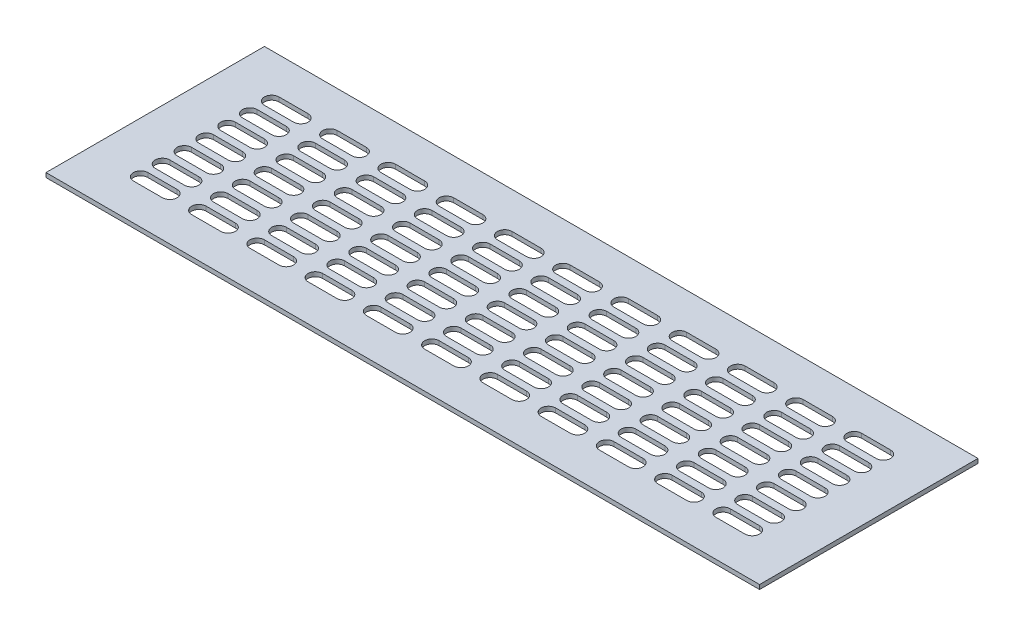
SolidWorks part; units mm, degrees
material "AISI 316 Stainless Steel Sheet (SS)"
ref_plane "Front Plane" through (0, 0, 0) normal (0, 0, 1) x (1, 0, 0)
ref_plane "Top Plane" through (0, 0, 0) normal (0, 1, 0) x (1, 0, 0)
ref_plane "Right Plane" through (0, 0, 0) normal (1, 0, 0) x (0, 0, -1)
sketch "Sketch1" plane through (0, 0, 0) normal (0, 1, 0) x (1, 0, 0)
  line L1 (-245, -75) -> (245, -75)
  line L2 (-245, -75) -> (-245, 75)
  line L3 (-245, 75) -> (245, 75)
  line L4 (245, -75) -> (245, 75)
  line L5 (-245, -75) -> (245, 75) construction
  line L6 (-245, 75) -> (245, -75) construction
  point P0 (0, 0)
  dimension "D1" = 490
  dimension "D2" = 150
extrude "Boss-Extrude1" add sketch "Sketch1" along normal mid plane 3
sketch "Sketch2" plane through (0, 1.5, 0) normal (0, 1, 0) x (1, 0, 0)
  line L0 (-210, 45) -> (-190, 45) construction
  line L1 (-210, 50) -> (-190, 50)
  line L2 (-210, 40) -> (-190, 40)
  line L3 (-245, 75) -> (-245, -75) construction
  line L4 (245, 75) -> (-245, 75) construction
  line L5 (-200, 55.9106) -> (-200, 34.5617) construction
  line L6 (-181.2775, 45) -> (-218.1008, 45) construction
  line L7 (-170, 45) -> (-150, 45) construction
  line L8 (-170, 50) -> (-150, 50)
  line L9 (-170, 40) -> (-150, 40)
  line L10 (-130, 45) -> (-110, 45) construction
  line L11 (-130, 50) -> (-110, 50)
  line L12 (-130, 40) -> (-110, 40)
  line L13 (-90, 45) -> (-70, 45) construction
  line L14 (-90, 50) -> (-70, 50)
  line L15 (-90, 40) -> (-70, 40)
  line L16 (-50, 45) -> (-30, 45) construction
  line L17 (-50, 50) -> (-30, 50)
  line L18 (-50, 40) -> (-30, 40)
  line L19 (-10, 45) -> (10, 45) construction
  line L20 (-10, 50) -> (10, 50)
  line L21 (-10, 40) -> (10, 40)
  line L22 (30, 45) -> (50, 45) construction
  line L23 (30, 50) -> (50, 50)
  line L24 (30, 40) -> (50, 40)
  line L25 (70, 45) -> (90, 45) construction
  line L26 (70, 50) -> (90, 50)
  line L27 (70, 40) -> (90, 40)
  line L28 (110, 45) -> (130, 45) construction
  line L29 (110, 50) -> (130, 50)
  line L30 (110, 40) -> (130, 40)
  line L31 (150, 45) -> (170, 45) construction
  line L32 (150, 50) -> (170, 50)
  line L33 (150, 40) -> (170, 40)
  line L34 (190, 45) -> (210, 45) construction
  line L35 (190, 50) -> (210, 50)
  line L36 (190, 40) -> (210, 40)
  line L37 (-170, 30) -> (-150, 30) construction
  line L38 (-170, 35) -> (-150, 35)
  line L39 (-170, 25) -> (-150, 25)
  line L40 (-130, 30) -> (-110, 30) construction
  line L41 (-130, 35) -> (-110, 35)
  line L42 (-130, 25) -> (-110, 25)
  line L43 (-90, 30) -> (-70, 30) construction
  line L44 (-90, 35) -> (-70, 35)
  line L45 (-90, 25) -> (-70, 25)
  line L46 (-50, 30) -> (-30, 30) construction
  line L47 (-50, 35) -> (-30, 35)
  line L48 (-50, 25) -> (-30, 25)
  line L49 (-10, 30) -> (10, 30) construction
  line L50 (-10, 35) -> (10, 35)
  line L51 (-10, 25) -> (10, 25)
  line L52 (30, 30) -> (50, 30) construction
  line L53 (30, 35) -> (50, 35)
  line L54 (30, 25) -> (50, 25)
  line L55 (70, 30) -> (90, 30) construction
  line L56 (70, 35) -> (90, 35)
  line L57 (70, 25) -> (90, 25)
  line L58 (110, 30) -> (130, 30) construction
  line L59 (110, 35) -> (130, 35)
  line L60 (110, 25) -> (130, 25)
  line L61 (150, 30) -> (170, 30) construction
  line L62 (150, 35) -> (170, 35)
  line L63 (150, 25) -> (170, 25)
  line L64 (190, 30) -> (210, 30) construction
  line L65 (190, 35) -> (210, 35)
  line L66 (190, 25) -> (210, 25)
  line L67 (-170, 15) -> (-150, 15) construction
  line L68 (-170, 20) -> (-150, 20)
  line L69 (-170, 10) -> (-150, 10)
  line L70 (-130, 15) -> (-110, 15) construction
  line L71 (-130, 20) -> (-110, 20)
  line L72 (-130, 10) -> (-110, 10)
  line L73 (-90, 15) -> (-70, 15) construction
  line L74 (-90, 20) -> (-70, 20)
  line L75 (-90, 10) -> (-70, 10)
  line L76 (-50, 15) -> (-30, 15) construction
  line L77 (-50, 20) -> (-30, 20)
  line L78 (-50, 10) -> (-30, 10)
  line L79 (-10, 15) -> (10, 15) construction
  line L80 (-10, 20) -> (10, 20)
  line L81 (-10, 10) -> (10, 10)
  line L82 (30, 15) -> (50, 15) construction
  line L83 (30, 20) -> (50, 20)
  line L84 (30, 10) -> (50, 10)
  line L85 (70, 15) -> (90, 15) construction
  line L86 (70, 20) -> (90, 20)
  line L87 (70, 10) -> (90, 10)
  line L88 (110, 15) -> (130, 15) construction
  line L89 (110, 20) -> (130, 20)
  line L90 (110, 10) -> (130, 10)
  line L91 (150, 15) -> (170, 15) construction
  line L92 (150, 20) -> (170, 20)
  line L93 (150, 10) -> (170, 10)
  line L94 (190, 15) -> (210, 15) construction
  line L95 (190, 20) -> (210, 20)
  line L96 (190, 10) -> (210, 10)
  line L97 (-170, 0) -> (-150, 0) construction
  line L98 (-170, 5) -> (-150, 5)
  line L99 (-170, -5) -> (-150, -5)
  line L100 (-130, 0) -> (-110, 0) construction
  line L101 (-130, 5) -> (-110, 5)
  line L102 (-130, -5) -> (-110, -5)
  line L103 (-90, 0) -> (-70, 0) construction
  line L104 (-90, 5) -> (-70, 5)
  line L105 (-90, -5) -> (-70, -5)
  line L106 (-50, 0) -> (-30, 0) construction
  line L107 (-50, 5) -> (-30, 5)
  line L108 (-50, -5) -> (-30, -5)
  line L109 (-10, 0) -> (10, 0) construction
  line L110 (-10, 5) -> (10, 5)
  line L111 (-10, -5) -> (10, -5)
  line L112 (30, 0) -> (50, 0) construction
  line L113 (30, 5) -> (50, 5)
  line L114 (30, -5) -> (50, -5)
  line L115 (70, 0) -> (90, 0) construction
  line L116 (70, 5) -> (90, 5)
  line L117 (70, -5) -> (90, -5)
  line L118 (110, 0) -> (130, 0) construction
  line L119 (110, 5) -> (130, 5)
  line L120 (110, -5) -> (130, -5)
  line L121 (150, 0) -> (170, 0) construction
  line L122 (150, 5) -> (170, 5)
  line L123 (150, -5) -> (170, -5)
  line L124 (190, 0) -> (210, 0) construction
  line L125 (190, 5) -> (210, 5)
  line L126 (190, -5) -> (210, -5)
  line L127 (-170, -15) -> (-150, -15) construction
  line L128 (-170, -10) -> (-150, -10)
  line L129 (-170, -20) -> (-150, -20)
  line L130 (-130, -15) -> (-110, -15) construction
  line L131 (-130, -10) -> (-110, -10)
  line L132 (-130, -20) -> (-110, -20)
  line L133 (-90, -15) -> (-70, -15) construction
  line L134 (-90, -10) -> (-70, -10)
  line L135 (-90, -20) -> (-70, -20)
  line L136 (-50, -15) -> (-30, -15) construction
  line L137 (-50, -10) -> (-30, -10)
  line L138 (-50, -20) -> (-30, -20)
  line L139 (-10, -15) -> (10, -15) construction
  line L140 (-10, -10) -> (10, -10)
  line L141 (-10, -20) -> (10, -20)
  line L142 (30, -15) -> (50, -15) construction
  line L143 (30, -10) -> (50, -10)
  line L144 (30, -20) -> (50, -20)
  line L145 (70, -15) -> (90, -15) construction
  line L146 (70, -10) -> (90, -10)
  line L147 (70, -20) -> (90, -20)
  line L148 (110, -15) -> (130, -15) construction
  line L149 (110, -10) -> (130, -10)
  line L150 (110, -20) -> (130, -20)
  line L151 (150, -15) -> (170, -15) construction
  line L152 (150, -10) -> (170, -10)
  line L153 (150, -20) -> (170, -20)
  line L154 (190, -15) -> (210, -15) construction
  line L155 (190, -10) -> (210, -10)
  line L156 (190, -20) -> (210, -20)
  line L157 (-170, -30) -> (-150, -30) construction
  line L158 (-170, -25) -> (-150, -25)
  line L159 (-170, -35) -> (-150, -35)
  line L160 (-130, -30) -> (-110, -30) construction
  line L161 (-130, -25) -> (-110, -25)
  line L162 (-130, -35) -> (-110, -35)
  line L163 (-90, -30) -> (-70, -30) construction
  line L164 (-90, -25) -> (-70, -25)
  line L165 (-90, -35) -> (-70, -35)
  line L166 (-50, -30) -> (-30, -30) construction
  line L167 (-50, -25) -> (-30, -25)
  line L168 (-50, -35) -> (-30, -35)
  line L169 (-10, -30) -> (10, -30) construction
  line L170 (-10, -25) -> (10, -25)
  line L171 (-10, -35) -> (10, -35)
  line L172 (30, -30) -> (50, -30) construction
  line L173 (30, -25) -> (50, -25)
  line L174 (30, -35) -> (50, -35)
  line L175 (70, -30) -> (90, -30) construction
  line L176 (70, -25) -> (90, -25)
  line L177 (70, -35) -> (90, -35)
  line L178 (110, -30) -> (130, -30) construction
  line L179 (110, -25) -> (130, -25)
  line L180 (110, -35) -> (130, -35)
  line L181 (150, -30) -> (170, -30) construction
  line L182 (150, -25) -> (170, -25)
  line L183 (150, -35) -> (170, -35)
  line L184 (190, -30) -> (210, -30) construction
  line L185 (190, -25) -> (210, -25)
  line L186 (190, -35) -> (210, -35)
  line L187 (-170, -45) -> (-150, -45) construction
  line L188 (-170, -40) -> (-150, -40)
  line L189 (-170, -50) -> (-150, -50)
  line L190 (-130, -45) -> (-110, -45) construction
  line L191 (-130, -40) -> (-110, -40)
  line L192 (-130, -50) -> (-110, -50)
  line L193 (-90, -45) -> (-70, -45) construction
  line L194 (-90, -40) -> (-70, -40)
  line L195 (-90, -50) -> (-70, -50)
  line L196 (-50, -45) -> (-30, -45) construction
  line L197 (-50, -40) -> (-30, -40)
  line L198 (-50, -50) -> (-30, -50)
  line L199 (-10, -45) -> (10, -45) construction
  line L200 (-10, -40) -> (10, -40)
  line L201 (-10, -50) -> (10, -50)
  line L202 (30, -45) -> (50, -45) construction
  line L203 (30, -40) -> (50, -40)
  line L204 (30, -50) -> (50, -50)
  line L205 (70, -45) -> (90, -45) construction
  line L206 (70, -40) -> (90, -40)
  line L207 (70, -50) -> (90, -50)
  line L208 (110, -45) -> (130, -45) construction
  line L209 (110, -40) -> (130, -40)
  line L210 (110, -50) -> (130, -50)
  line L211 (150, -45) -> (170, -45) construction
  line L212 (150, -40) -> (170, -40)
  line L213 (150, -50) -> (170, -50)
  line L214 (190, -45) -> (210, -45) construction
  line L215 (190, -40) -> (210, -40)
  line L216 (190, -50) -> (210, -50)
  line L217 (-210, 30) -> (-190, 30) construction
  line L218 (-210, 35) -> (-190, 35)
  line L219 (-210, 25) -> (-190, 25)
  line L220 (-210, 15) -> (-190, 15) construction
  line L221 (-210, 20) -> (-190, 20)
  line L222 (-210, 10) -> (-190, 10)
  line L223 (-210, 0) -> (-190, 0) construction
  line L224 (-210, 5) -> (-190, 5)
  line L225 (-210, -5) -> (-190, -5)
  line L226 (-210, -15) -> (-190, -15) construction
  line L227 (-210, -10) -> (-190, -10)
  line L228 (-210, -20) -> (-190, -20)
  line L229 (-210, -30) -> (-190, -30) construction
  line L230 (-210, -25) -> (-190, -25)
  line L231 (-210, -35) -> (-190, -35)
  line L232 (-210, -45) -> (-190, -45) construction
  line L233 (-210, -40) -> (-190, -40)
  line L234 (-210, -50) -> (-190, -50)
  arc A0 (-210, 50) -> (-210, 40) centre (-210, 45) ccw
  arc A1 (-190, 40) -> (-190, 50) centre (-190, 45) ccw
  arc A2 (-170, 50) -> (-170, 40) centre (-170, 45) ccw
  arc A3 (-150, 40) -> (-150, 50) centre (-150, 45) ccw
  arc A4 (-130, 50) -> (-130, 40) centre (-130, 45) ccw
  arc A5 (-110, 40) -> (-110, 50) centre (-110, 45) ccw
  arc A6 (-90, 50) -> (-90, 40) centre (-90, 45) ccw
  arc A7 (-70, 40) -> (-70, 50) centre (-70, 45) ccw
  arc A8 (-50, 50) -> (-50, 40) centre (-50, 45) ccw
  arc A9 (-30, 40) -> (-30, 50) centre (-30, 45) ccw
  arc A10 (-10, 50) -> (-10, 40) centre (-10, 45) ccw
  arc A11 (10, 40) -> (10, 50) centre (10, 45) ccw
  arc A12 (30, 50) -> (30, 40) centre (30, 45) ccw
  arc A13 (50, 40) -> (50, 50) centre (50, 45) ccw
  arc A14 (70, 50) -> (70, 40) centre (70, 45) ccw
  arc A15 (90, 40) -> (90, 50) centre (90, 45) ccw
  arc A16 (110, 50) -> (110, 40) centre (110, 45) ccw
  arc A17 (130, 40) -> (130, 50) centre (130, 45) ccw
  arc A18 (150, 50) -> (150, 40) centre (150, 45) ccw
  arc A19 (170, 40) -> (170, 50) centre (170, 45) ccw
  arc A20 (190, 50) -> (190, 40) centre (190, 45) ccw
  arc A21 (210, 40) -> (210, 50) centre (210, 45) ccw
  arc A22 (-170, 35) -> (-170, 25) centre (-170, 30) ccw
  arc A23 (-150, 25) -> (-150, 35) centre (-150, 30) ccw
  arc A24 (-130, 35) -> (-130, 25) centre (-130, 30) ccw
  arc A25 (-110, 25) -> (-110, 35) centre (-110, 30) ccw
  arc A26 (-90, 35) -> (-90, 25) centre (-90, 30) ccw
  arc A27 (-70, 25) -> (-70, 35) centre (-70, 30) ccw
  arc A28 (-50, 35) -> (-50, 25) centre (-50, 30) ccw
  arc A29 (-30, 25) -> (-30, 35) centre (-30, 30) ccw
  arc A30 (-10, 35) -> (-10, 25) centre (-10, 30) ccw
  arc A31 (10, 25) -> (10, 35) centre (10, 30) ccw
  arc A32 (30, 35) -> (30, 25) centre (30, 30) ccw
  arc A33 (50, 25) -> (50, 35) centre (50, 30) ccw
  arc A34 (70, 35) -> (70, 25) centre (70, 30) ccw
  arc A35 (90, 25) -> (90, 35) centre (90, 30) ccw
  arc A36 (110, 35) -> (110, 25) centre (110, 30) ccw
  arc A37 (130, 25) -> (130, 35) centre (130, 30) ccw
  arc A38 (150, 35) -> (150, 25) centre (150, 30) ccw
  arc A39 (170, 25) -> (170, 35) centre (170, 30) ccw
  arc A40 (190, 35) -> (190, 25) centre (190, 30) ccw
  arc A41 (210, 25) -> (210, 35) centre (210, 30) ccw
  arc A42 (-170, 20) -> (-170, 10) centre (-170, 15) ccw
  arc A43 (-150, 10) -> (-150, 20) centre (-150, 15) ccw
  arc A44 (-130, 20) -> (-130, 10) centre (-130, 15) ccw
  arc A45 (-110, 10) -> (-110, 20) centre (-110, 15) ccw
  arc A46 (-90, 20) -> (-90, 10) centre (-90, 15) ccw
  arc A47 (-70, 10) -> (-70, 20) centre (-70, 15) ccw
  arc A48 (-50, 20) -> (-50, 10) centre (-50, 15) ccw
  arc A49 (-30, 10) -> (-30, 20) centre (-30, 15) ccw
  arc A50 (-10, 20) -> (-10, 10) centre (-10, 15) ccw
  arc A51 (10, 10) -> (10, 20) centre (10, 15) ccw
  arc A52 (30, 20) -> (30, 10) centre (30, 15) ccw
  arc A53 (50, 10) -> (50, 20) centre (50, 15) ccw
  arc A54 (70, 20) -> (70, 10) centre (70, 15) ccw
  arc A55 (90, 10) -> (90, 20) centre (90, 15) ccw
  arc A56 (110, 20) -> (110, 10) centre (110, 15) ccw
  arc A57 (130, 10) -> (130, 20) centre (130, 15) ccw
  arc A58 (150, 20) -> (150, 10) centre (150, 15) ccw
  arc A59 (170, 10) -> (170, 20) centre (170, 15) ccw
  arc A60 (190, 20) -> (190, 10) centre (190, 15) ccw
  arc A61 (210, 10) -> (210, 20) centre (210, 15) ccw
  arc A62 (-170, 5) -> (-170, -5) centre (-170, 0) ccw
  arc A63 (-150, -5) -> (-150, 5) centre (-150, 0) ccw
  arc A64 (-130, 5) -> (-130, -5) centre (-130, 0) ccw
  arc A65 (-110, -5) -> (-110, 5) centre (-110, 0) ccw
  arc A66 (-90, 5) -> (-90, -5) centre (-90, 0) ccw
  arc A67 (-70, -5) -> (-70, 5) centre (-70, 0) ccw
  arc A68 (-50, 5) -> (-50, -5) centre (-50, 0) ccw
  arc A69 (-30, -5) -> (-30, 5) centre (-30, 0) ccw
  arc A70 (-10, 5) -> (-10, -5) centre (-10, 0) ccw
  arc A71 (10, -5) -> (10, 5) centre (10, 0) ccw
  arc A72 (30, 5) -> (30, -5) centre (30, 0) ccw
  arc A73 (50, -5) -> (50, 5) centre (50, 0) ccw
  arc A74 (70, 5) -> (70, -5) centre (70, 0) ccw
  arc A75 (90, -5) -> (90, 5) centre (90, 0) ccw
  arc A76 (110, 5) -> (110, -5) centre (110, 0) ccw
  arc A77 (130, -5) -> (130, 5) centre (130, 0) ccw
  arc A78 (150, 5) -> (150, -5) centre (150, 0) ccw
  arc A79 (170, -5) -> (170, 5) centre (170, 0) ccw
  arc A80 (190, 5) -> (190, -5) centre (190, 0) ccw
  arc A81 (210, -5) -> (210, 5) centre (210, 0) ccw
  arc A82 (-170, -10) -> (-170, -20) centre (-170, -15) ccw
  arc A83 (-150, -20) -> (-150, -10) centre (-150, -15) ccw
  arc A84 (-130, -10) -> (-130, -20) centre (-130, -15) ccw
  arc A85 (-110, -20) -> (-110, -10) centre (-110, -15) ccw
  arc A86 (-90, -10) -> (-90, -20) centre (-90, -15) ccw
  arc A87 (-70, -20) -> (-70, -10) centre (-70, -15) ccw
  arc A88 (-50, -10) -> (-50, -20) centre (-50, -15) ccw
  arc A89 (-30, -20) -> (-30, -10) centre (-30, -15) ccw
  arc A90 (-10, -10) -> (-10, -20) centre (-10, -15) ccw
  arc A91 (10, -20) -> (10, -10) centre (10, -15) ccw
  arc A92 (30, -10) -> (30, -20) centre (30, -15) ccw
  arc A93 (50, -20) -> (50, -10) centre (50, -15) ccw
  arc A94 (70, -10) -> (70, -20) centre (70, -15) ccw
  arc A95 (90, -20) -> (90, -10) centre (90, -15) ccw
  arc A96 (110, -10) -> (110, -20) centre (110, -15) ccw
  arc A97 (130, -20) -> (130, -10) centre (130, -15) ccw
  arc A98 (150, -10) -> (150, -20) centre (150, -15) ccw
  arc A99 (170, -20) -> (170, -10) centre (170, -15) ccw
  arc A100 (190, -10) -> (190, -20) centre (190, -15) ccw
  arc A101 (210, -20) -> (210, -10) centre (210, -15) ccw
  arc A102 (-170, -25) -> (-170, -35) centre (-170, -30) ccw
  arc A103 (-150, -35) -> (-150, -25) centre (-150, -30) ccw
  arc A104 (-130, -25) -> (-130, -35) centre (-130, -30) ccw
  arc A105 (-110, -35) -> (-110, -25) centre (-110, -30) ccw
  arc A106 (-90, -25) -> (-90, -35) centre (-90, -30) ccw
  arc A107 (-70, -35) -> (-70, -25) centre (-70, -30) ccw
  arc A108 (-50, -25) -> (-50, -35) centre (-50, -30) ccw
  arc A109 (-30, -35) -> (-30, -25) centre (-30, -30) ccw
  arc A110 (-10, -25) -> (-10, -35) centre (-10, -30) ccw
  arc A111 (10, -35) -> (10, -25) centre (10, -30) ccw
  arc A112 (30, -25) -> (30, -35) centre (30, -30) ccw
  arc A113 (50, -35) -> (50, -25) centre (50, -30) ccw
  arc A114 (70, -25) -> (70, -35) centre (70, -30) ccw
  arc A115 (90, -35) -> (90, -25) centre (90, -30) ccw
  arc A116 (110, -25) -> (110, -35) centre (110, -30) ccw
  arc A117 (130, -35) -> (130, -25) centre (130, -30) ccw
  arc A118 (150, -25) -> (150, -35) centre (150, -30) ccw
  arc A119 (170, -35) -> (170, -25) centre (170, -30) ccw
  arc A120 (190, -25) -> (190, -35) centre (190, -30) ccw
  arc A121 (210, -35) -> (210, -25) centre (210, -30) ccw
  arc A122 (-170, -40) -> (-170, -50) centre (-170, -45) ccw
  arc A123 (-150, -50) -> (-150, -40) centre (-150, -45) ccw
  arc A124 (-130, -40) -> (-130, -50) centre (-130, -45) ccw
  arc A125 (-110, -50) -> (-110, -40) centre (-110, -45) ccw
  arc A126 (-90, -40) -> (-90, -50) centre (-90, -45) ccw
  arc A127 (-70, -50) -> (-70, -40) centre (-70, -45) ccw
  arc A128 (-50, -40) -> (-50, -50) centre (-50, -45) ccw
  arc A129 (-30, -50) -> (-30, -40) centre (-30, -45) ccw
  arc A130 (-10, -40) -> (-10, -50) centre (-10, -45) ccw
  arc A131 (10, -50) -> (10, -40) centre (10, -45) ccw
  arc A132 (30, -40) -> (30, -50) centre (30, -45) ccw
  arc A133 (50, -50) -> (50, -40) centre (50, -45) ccw
  arc A134 (70, -40) -> (70, -50) centre (70, -45) ccw
  arc A135 (90, -50) -> (90, -40) centre (90, -45) ccw
  arc A136 (110, -40) -> (110, -50) centre (110, -45) ccw
  arc A137 (130, -50) -> (130, -40) centre (130, -45) ccw
  arc A138 (150, -40) -> (150, -50) centre (150, -45) ccw
  arc A139 (170, -50) -> (170, -40) centre (170, -45) ccw
  arc A140 (190, -40) -> (190, -50) centre (190, -45) ccw
  arc A141 (210, -50) -> (210, -40) centre (210, -45) ccw
  arc A142 (-210, 35) -> (-210, 25) centre (-210, 30) ccw
  arc A143 (-190, 25) -> (-190, 35) centre (-190, 30) ccw
  arc A144 (-210, 20) -> (-210, 10) centre (-210, 15) ccw
  arc A145 (-190, 10) -> (-190, 20) centre (-190, 15) ccw
  arc A146 (-210, 5) -> (-210, -5) centre (-210, 0) ccw
  arc A147 (-190, -5) -> (-190, 5) centre (-190, 0) ccw
  arc A148 (-210, -10) -> (-210, -20) centre (-210, -15) ccw
  arc A149 (-190, -20) -> (-190, -10) centre (-190, -15) ccw
  arc A150 (-210, -25) -> (-210, -35) centre (-210, -30) ccw
  arc A151 (-190, -35) -> (-190, -25) centre (-190, -30) ccw
  arc A152 (-210, -40) -> (-210, -50) centre (-210, -45) ccw
  arc A153 (-190, -50) -> (-190, -40) centre (-190, -45) ccw
  point P2 (-200, 45)
  point P20 (-160, 45)
  point P27 (-120, 45)
  point P34 (-80, 45)
  point P41 (-40, 45)
  point P48 (0, 45)
  point P55 (40, 45)
  point P62 (80, 45)
  point P69 (120, 45)
  point P76 (160, 45)
  point P83 (200, 45)
  point P90 (-160, 30)
  point P97 (-120, 30)
  point P104 (-80, 30)
  point P111 (-40, 30)
  point P118 (0, 30)
  point P125 (40, 30)
  point P132 (80, 30)
  point P139 (120, 30)
  point P146 (160, 30)
  point P153 (200, 30)
  point P160 (-160, 15)
  point P167 (-120, 15)
  point P174 (-80, 15)
  point P181 (-40, 15)
  point P188 (0, 15)
  point P195 (40, 15)
  point P202 (80, 15)
  point P209 (120, 15)
  point P216 (160, 15)
  point P223 (200, 15)
  point P230 (-160, 0)
  point P237 (-120, 0)
  point P244 (-80, 0)
  point P251 (-40, 0)
  point P258 (0, 0)
  point P265 (40, 0)
  point P272 (80, 0)
  point P279 (120, 0)
  point P286 (160, 0)
  point P293 (200, 0)
  point P300 (-160, -15)
  point P307 (-120, -15)
  point P314 (-80, -15)
  point P321 (-40, -15)
  point P328 (0, -15)
  point P335 (40, -15)
  point P342 (80, -15)
  point P349 (120, -15)
  point P356 (160, -15)
  point P363 (200, -15)
  point P370 (-160, -30)
  point P377 (-120, -30)
  point P384 (-80, -30)
  point P391 (-40, -30)
  point P398 (0, -30)
  point P405 (40, -30)
  point P412 (80, -30)
  point P419 (120, -30)
  point P426 (160, -30)
  point P433 (200, -30)
  point P440 (-160, -45)
  point P447 (-120, -45)
  point P454 (-80, -45)
  point P461 (-40, -45)
  point P468 (0, -45)
  point P475 (40, -45)
  point P482 (80, -45)
  point P489 (120, -45)
  point P496 (160, -45)
  point P503 (200, -45)
  point P510 (-200, 30)
  point P517 (-200, 15)
  point P524 (-200, 0)
  point P531 (-200, -15)
  point P538 (-200, -30)
  point P545 (-200, -45)
  dimension "D3" = 5
  dimension "D1" = 35
  dimension "D2" = 30
  dimension "D4" = 20
extrude "Cut-Extrude1" cut sketch "Sketch2" against normal through all
